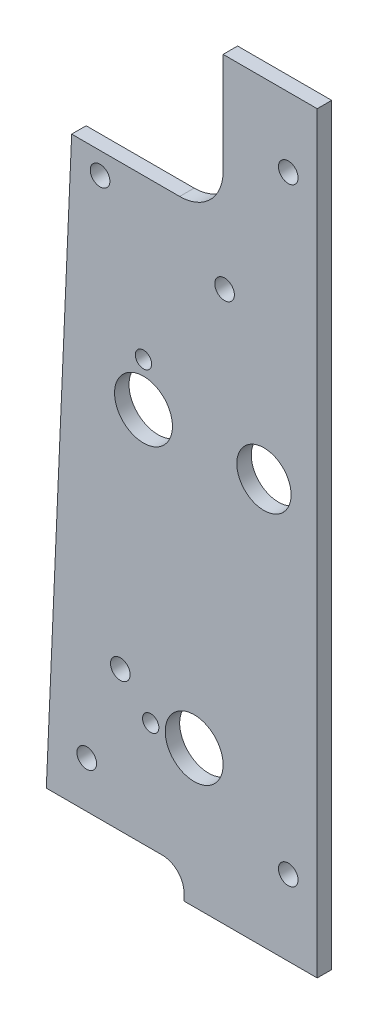
SolidWorks part; units mm, degrees
material "Acrylic (Medium-high impact)"
ref_plane "Front Plane" through (0, 0, 0) normal (0, 0, 1) x (1, 0, 0)
ref_plane "Top Plane" through (0, 0, 0) normal (0, 1, 0) x (1, 0, 0)
ref_plane "Right Plane" through (0, 0, 0) normal (1, 0, 0) x (0, 0, -1)
sketch "Sketch1" plane through (0, 0, 0) normal (0, 0, 1) x (1, 0, 0)
  line L8 (-29.21, 1.5875) -> (-29.21, 0)
  line L9 (-29.21, 0) -> (0, 0)
  line L10 (0, 0) -> (0, 165.1)
  line L11 (0, 165.1) -> (-25.4, 165.1)
  line L12 (-25.4, 165.1) -> (-25.4, 138.1125)
  line L13 (-30.1625, 133.35) -> (-53.848, 133.35)
  line L14 (-53.848, 133.35) -> (-59.4118, 6.35)
  line L15 (-59.4118, 6.35) -> (-33.9725, 6.35)
  line L16 (-29.21, 1.5875) -> (-29.21, 0)
  line L17 (-29.21, 0) -> (0, 0)
  line L18 (0, 0) -> (0, 165.1)
  line L19 (0, 165.1) -> (-25.4, 165.1)
  line L20 (-25.4, 165.1) -> (-25.4, 138.1125)
  line L21 (-30.1625, 133.35) -> (-53.848, 133.35)
  line L22 (-53.848, 133.35) -> (-59.4118, 6.35)
  line L23 (-59.4118, 6.35) -> (-33.9725, 6.35)
  arc A2 (-29.21, 1.5875) -> (-33.9725, 6.35) centre (-33.9725, 1.5875) ccw
  arc A3 (-30.1625, 133.35) -> (-25.4, 138.1125) centre (-30.1625, 138.1125) ccw
  arc A4 (-29.21, 1.5875) -> (-33.9725, 6.35) centre (-33.9725, 1.5875) ccw
  arc A5 (-30.1625, 133.35) -> (-25.4, 138.1125) centre (-30.1625, 138.1125) ccw
  dimension "D1" = 0
extrude "Boss-Extrude1" add sketch "Sketch1" against normal blind 3.175
hole_wizard "#6 Clearance Hole1" positions "Sketch3" profile "Sketch2" hole size "#6" standard "ANSI Inch" end condition through all
sketch "Sketch3" plane through (0, 0, 0) normal (0, 0, 1) x (1, 0, 0)
  point P0 (-47.625, 128.5875)
  point P3 (-6.35, 149.86)
  point P6 (-50.546, 16.51)
  point P9 (-6.35, 16.51)
sketch "Sketch2" plane through (-47.625, 128.5875, 0) normal (1, 0, 0) x (0, -1, 0)
  line L0 (0, 0) -> (0, 3.175)
  line L1 (0, 3.175) -> (2.1526, 3.175)
  line L2 (2.1526, 3.175) -> (2.1526, 0)
  line L5 (2.1526, 0) -> (0, 0)
  line L11 (0, -6.35) -> (0, 107.95) construction
  dimension "Thru Hole Dia." = 4.3053
  dimension "Thru Hole Depth" = 3.175
hole_wizard "#6 Clearance Hole2" positions "Sketch5" profile "Sketch4" hole size "#6" standard "ANSI Inch" end condition through all
sketch "Sketch5" plane through (0, 0, 0) normal (0, 0, 1) x (1, 0, 0)
  point P0 (-43.18, 37.084)
  point P3 (-20.32, 120.65)
sketch "Sketch4" plane through (-43.18, 37.084, 0) normal (1, 0, 0) x (0, -1, 0)
  line L0 (0, 0) -> (0, 3.175)
  line L1 (0, 3.175) -> (2.1526, 3.175)
  line L2 (2.1526, 3.175) -> (2.1526, 0)
  line L5 (2.1526, 0) -> (0, 0)
  line L11 (0, -6.35) -> (0, 107.95) construction
  dimension "Thru Hole Dia." = 4.3053
  dimension "Thru Hole Depth" = 3.175
hole_wizard "9/64 (0.14063) Diameter Hole1" positions "Sketch7" profile "Sketch6" hole size "9/64" standard "ANSI Inch" end condition through all
sketch "Sketch7" plane through (0, 0, 0) normal (0, 0, 1) x (1, 0, 0)
  point P0 (-38.1, 98.425)
  point P3 (-36.5125, 30.1625)
sketch "Sketch6" plane through (-38.1, 98.425, 0) normal (1, 0, 0) x (0, -1, 0)
  line L0 (0, 0) -> (0, 3.175)
  line L1 (0, 3.175) -> (1.786, 3.175)
  line L2 (1.786, 3.175) -> (1.786, 0)
  line L5 (1.786, 0) -> (0, 0)
  line L11 (0, -6.35) -> (0, 107.95) construction
  dimension "Thru Hole Dia." = 3.572
  dimension "Thru Hole Depth" = 3.175
hole_wizard "15/32 (0.46875) Diameter Hole1" positions "Sketch9" profile "Sketch8" hole size "15/32" standard "ANSI Inch" end condition through all
sketch "Sketch9" plane through (0, 0, 0) normal (0, 0, 1) x (1, 0, 0)
  point P0 (-11.684, 88.9)
sketch "Sketch8" plane through (-11.684, 88.9, 0) normal (1, 0, 0) x (0, -1, 0)
  line L0 (0, 0) -> (0, 3.175)
  line L1 (0, 3.175) -> (5.9531, 3.175)
  line L2 (5.9531, 3.175) -> (5.9531, 0)
  line L5 (5.9531, 0) -> (0, 0)
  line L11 (0, -6.35) -> (0, 107.95) construction
  dimension "Thru Hole Dia." = 11.9062
  dimension "Thru Hole Depth" = 3.175
hole_wizard "1/2 (0.5) Diameter Hole1" positions "Sketch11" profile "Sketch10" hole size "1/2" standard "ANSI Inch" end condition through all
sketch "Sketch11" plane through (0, 0, 0) normal (0, 0, 1) x (1, 0, 0)
  point P0 (-38.1, 88.9)
  point P3 (-26.9875, 30.1625)
sketch "Sketch10" plane through (-38.1, 88.9, 0) normal (1, 0, 0) x (0, -1, 0)
  line L0 (0, 0) -> (0, 3.175)
  line L1 (0, 3.175) -> (6.35, 3.175)
  line L2 (6.35, 3.175) -> (6.35, 0)
  line L5 (6.35, 0) -> (0, 0)
  line L11 (0, -6.35) -> (0, 107.95) construction
  dimension "Thru Hole Dia." = 12.7
  dimension "Thru Hole Depth" = 3.175
sketch "Sketch12" plane through (0, 0, 0) normal (0, 0, 1) x (1, 0, 0)
  line L0 (0, 165.1) -> (-25.4, 165.1) construction
  line L1 (-20.6375, 165.1) -> (-30.1625, 165.1)
  line L2 (-20.6375, 165.1) -> (-20.6375, 133.35)
  line L3 (-20.6375, 133.35) -> (-30.1625, 133.35)
  line L4 (-30.1625, 165.1) -> (-30.1625, 133.35)
  line L5 (-25.4, 165.1) -> (-25.4, 138.1125) construction
  dimension "D1" = 4.7625
extrude "Cut-Extrude1" cut sketch "Sketch12" against normal up to next
fillet "Fillet1" radius 9.525 1 edges at (-20.6375, 133.35, -1.5875)
